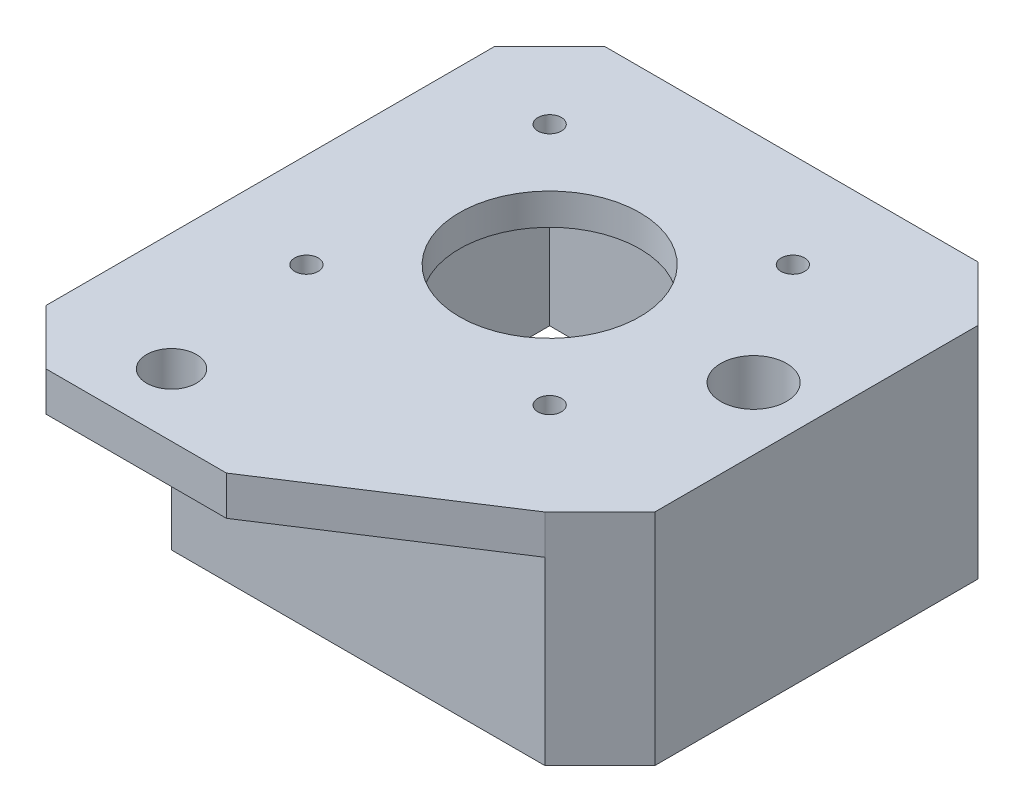
SolidWorks part; units mm, degrees
ref_plane "Front Plane" through (0, 0, 0) normal (0, 0, 1) x (1, 0, 0)
ref_plane "Top Plane" through (0, 0, 0) normal (0, 1, 0) x (1, 0, 0)
ref_plane "Right Plane" through (0, 0, 0) normal (1, 0, 0) x (0, 0, -1)
sketch "Sketch1" plane through (0, 0, 0) normal (0, 1, 0) x (1, 0, 0)
  line L0 (0, 21) -> (55, 21) construction
  line L1 (0, 0) -> (55, 0)
  line L2 (0, 0) -> (0, 42)
  line L3 (0, 42) -> (55, 42)
  line L4 (55, 0) -> (55, 42)
  line L5 (21, 42) -> (21, 0) construction
  circle A0 centre (47, 21) radius 4.2
  circle A1 centre (21, 21) radius 11.5
  circle A2 centre (5.5, 36.5) radius 1.5
  circle A3 centre (36.5, 36.5) radius 1.5
  circle A4 centre (5.5, 5.5) radius 1.5
  circle A5 centre (36.5, 5.5) radius 1.5
  point P8 (55, 21)
  dimension "D2" = 23
  dimension "D4" = 8.4
  dimension "D9" = 3
  dimension "D1" = 26
  dimension "D3" = 42
  dimension "D5" = 21
  dimension "D6" = 55
  dimension "D7" = 15.5
  dimension "D8" = 15.5
extrude "Boss-Extrude1" add sketch "Sketch1" along normal blind 4
sketch "Sketch2" plane through (0, 0, 0) normal (0, -1, 0) x (1, 0, 0)
  line L0 (0, 0) -> (55, 0) construction
  line L1 (40.4, 0) -> (42.25, 0)
  line L2 (40.4, 0) -> (40.4, -42)
  line L3 (40.4, -42) -> (42.25, -42)
  line L4 (42.25, 0) -> (42.25, -42)
  line L5 (55, -42) -> (0, -42) construction
  line L6 (55, 0) -> (55, -42) construction
  line L7 (55, -11) -> (42.25, -11)
  line L8 (55, -11) -> (55, -31)
  line L9 (55, -31) -> (42.25, -31)
  line L10 (42.25, -11) -> (42.25, -31)
  circle A0 centre (47, -21) radius 6.6
  circle A1 centre (47, -21) radius 4.2
  circle A2 centre (47, -21) radius 4.2 construction
  point P25 (55, -21)
  point P26 (55, -21)
  circle M7 centre (47, -21) radius 4.2
  line M10 (55, -42) -> (55, 0)
  dimension "D1" = 2.4
  dimension "D2" = 1.85
  dimension "D3" = 20
extrude "Boss-Extrude2" add sketch "Sketch2" along normal blind 20 contours L4 A0 L10 M7 | A0 L10 L9 L7 L4 M10
sketch "Sketch3" plane through (0, -20, 0) normal (0, -1, 0) x (1, 0, 0)
  line L1 (55, -31) -> (42.25, -31)
  line L2 (55, -31) -> (55, -11)
  line L3 (55, -11) -> (42.25, -11)
  line L4 (42.25, -31) -> (42.25, -11)
extrude "Boss-Extrude3" add sketch "Sketch3" along normal blind 4
sketch "Sketch4" plane through (0, 0, 0) normal (0, -1, 0) x (1, 0, 0)
  line L0 (42.25, -11) -> (42.25, -31) construction
  line L1 (42.25, 0.25) -> (-0.25, 0.25)
  line L2 (42.25, 0.25) -> (42.25, -42.25)
  line L3 (42.25, -42.25) -> (-0.25, -42.25)
  line L4 (-0.25, 0.25) -> (-0.25, -42.25)
  line L9 (48.6, 6.6) -> (-6.6, 6.6)
  line L10 (48.6, 6.6) -> (48.6, -48.6)
  line L11 (48.6, -48.6) -> (-6.6, -48.6)
  line L12 (-6.6, 6.6) -> (-6.6, -48.6)
  line L13 (55, -42) -> (0, -42) construction
  line L14 (0, -42) -> (0, 0) construction
  line L15 (0, 0) -> (55, 0) construction
  dimension "D1" = 0.25
  dimension "D2" = 0.25
  dimension "D3" = 0.25
  dimension "D4" = 6.35
  dimension "D5" = 6.35
  dimension "D6" = 6.35
  dimension "D7" = 6.35
extrude "Boss-Extrude4" add sketch "Sketch4" along normal up to surface (24 mm away) contours L10 L9 L12 L11 | L2 L1 L4 L3 up to face at (48.625, -24, -21)
sketch "Sketch5" plane through (0, 0, 0) normal (0, 1, 0) x (1, 0, 0)
  circle A0 centre (47, 21) radius 4.2
  circle A1 centre (47, 21) radius 4.2 construction
extrude "Cut-Extrude1" cut sketch "Sketch5" against normal up to surface (20 mm away) up to face at (49.9, -20, -21)
sketch "Sketch6" plane through (48.6, 0, 0) normal (1, 0, 0) x (0, 0, -1)
  line L0 (0, 4) -> (42, 4) construction
  line L1 (-6.6, 0) -> (0, 0)
  line L2 (-6.6, 0) -> (-6.6, 4)
  line L3 (-6.6, 4) -> (0, 4)
  line L4 (0, 0) -> (0, 4)
  line L5 (0, 4) -> (42, 4)
  line L6 (21, 4) -> (21, -2.4275) construction
  line L7 (48.6, 4) -> (42, 4)
  line L8 (42, 0) -> (42, 4)
  line L9 (48.6, 0) -> (42, 0)
  line L10 (48.6, 0) -> (48.6, 4)
  point P9 (21, 4)
  line M3 (0, 0) -> (-6.6, 0)
extrude "Boss-Extrude6" add sketch "Sketch6" against normal up to surface (48.6 mm away) contours L9 L10 L7 L8 | L4 L3 L2 M3 up to face at (0, 2, -21)
sketch "Sketch7" plane through (0, 0, -48.6) normal (0, 0, -1) x (-1, 0, 0)
  line L0 (6.6, -24) -> (6.6, 0) construction
  line L1 (0, 0) -> (6.6, 0)
  line L2 (0, 0) -> (0, 4)
  line L3 (0, 4) -> (6.6, 4)
  line L4 (6.6, 0) -> (6.6, 4)
extrude "Boss-Extrude7" add sketch "Sketch7" against normal up to surface (55.2 mm away) up to face at (14, -6.6667, 6.6)
sketch "Sketch8" plane through (48.6, 0, 0) normal (1, 0, 0) x (0, 0, -1)
  line L6 (42, 0) -> (31, 0)
  line L7 (31, 0) -> (31, -24)
  line L8 (31, -24) -> (48.6, -24)
  line L9 (48.6, -24) -> (48.6, 4)
  line L10 (48.6, 4) -> (42, 4)
  line L11 (42, 4) -> (42, 0)
  line L12 (42, 0) -> (31, 0)
  line L13 (31, 0) -> (31, -24)
  line L14 (31, -24) -> (48.6, -24)
  line L15 (48.6, -24) -> (48.6, 4)
  line L16 (48.6, 4) -> (42, 4)
  line L17 (42, 4) -> (42, 0)
  line L18 (11, -24) -> (11, 0)
  line L19 (11, 0) -> (0, 0)
  line L20 (0, 0) -> (0, 4)
  line L21 (0, 4) -> (-6.6, 4)
  line L22 (-6.6, 4) -> (-6.6, -24)
  line L23 (-6.6, -24) -> (11, -24)
  line L24 (11, -24) -> (11, 0)
  line L25 (11, 0) -> (0, 0)
  line L26 (0, 0) -> (0, 4)
  line L27 (0, 4) -> (-6.6, 4)
  line L28 (-6.6, 4) -> (-6.6, -24)
  line L29 (-6.6, -24) -> (11, -24)
  dimension "D1" = 0
  dimension "D2" = 0
extrude "Boss-Extrude8" add sketch "Sketch8" along normal up to surface (6.4 mm away) up to face at (55, -5, -21)
sketch "Sketch9" plane through (0, 4, 0) normal (0, 1, 0) x (1, 0, 0)
  line L0 (55, 0.4) -> (48, -6.6)
  line L1 (55, -6.6) -> (55, 48.6) construction
  line L2 (-6.6, -6.6) -> (55, -6.6) construction
  line L3 (48, -6.6) -> (55, -6.6)
  line L4 (55, -6.6) -> (55, 0.4)
  line L5 (55, 41.6) -> (48, 48.6)
  line L6 (-6.6, 48.6) -> (55, 48.6) construction
  line L7 (48, 48.6) -> (55, 48.6)
  line L8 (55, 48.6) -> (55, 41.6)
  line L9 (0.4, 48.6) -> (-6.6, 48.6)
  line L10 (-6.6, 48.6) -> (-6.6, 41.6)
  line L11 (-6.6, -6.6) -> (-6.6, 48.6) construction
  line L12 (-6.6, 41.6) -> (0.4, 48.6)
  line L13 (0.4, -6.6) -> (-6.6, 0.4)
  line L14 (-6.6, 0.4) -> (-6.6, -6.6)
  line L15 (-6.6, -6.6) -> (0.4, -6.6)
  dimension "D1" = 7
extrude "Cut-Extrude2" cut sketch "Sketch9" against normal up to surface (28 mm away) up to face at (24.2, -24, -21)
sketch "Sketch10" plane through (0, 4, 0) normal (0, 1, 0) x (1, 0, 0)
  line L0 (-6.6, 0.4) -> (-6.6, 41.6) construction
  line L1 (-6.6, 0.4) -> (23.4, 0.4)
  line L2 (-6.6, 0.4) -> (-6.6, -22.6)
  line L3 (-6.6, -22.6) -> (23.4, -22.6)
  line L4 (23.4, 0.4) -> (23.4, -22.6)
  line L5 (0.4, -6.6) -> (-6.6, 0.4) construction
  line L6 (23.4, -22.6) -> (48, -6.6)
  line L7 (48, -6.6) -> (23.4, -6.6)
  line L8 (0.4, -6.6) -> (48, -6.6) construction
  line L9 (23.4, -6.6) -> (23.4, -22.6)
  line L10 (-6.6, -15.6) -> (0.4, -22.6)
  circle A0 centre (8.4, -14.6) radius 3.175
  line M10 (-6.6, 0.4) -> (0.4, -6.6)
  line M11 (0.4, -6.6) -> (48, -6.6)
  dimension "D3" = 6.35
  dimension "D1" = 15
  dimension "D2" = 15
  dimension "D4" = 15
  dimension "D5" = 8
  dimension "D6" = 7
  dimension "D7" = 7
extrude "Boss-Extrude10" add sketch "Sketch10" against normal blind 5 contours L2 L10 L3 L4 A0 M11 M10 | L4 L6 M11
equation "\"8mm hole\" = 8.4mm"
equation "\"22mm hole\"= 23mm"
equation "\"D2@Sketch1\"=\"22mm hole\""
equation "\"D4@Sketch1\"=\"8mm hole\""
